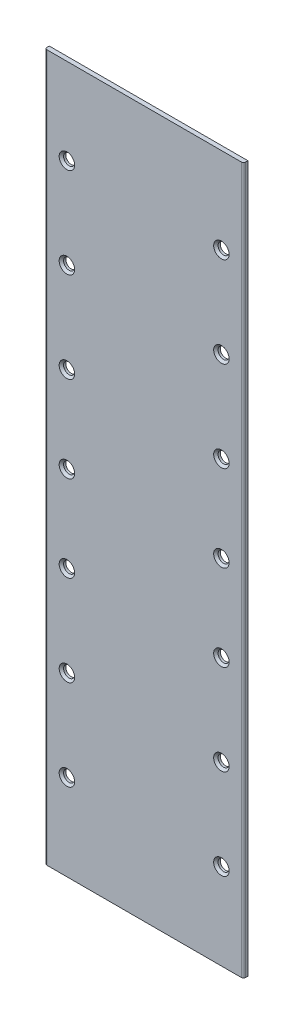
SolidWorks part; units mm, degrees
ref_plane "Plan de face" through (0, 0, 0) normal (0, 0, 1) x (1, 0, 0)
ref_plane "Plan de dessus" through (0, 0, 0) normal (0, 1, 0) x (1, 0, 0)
ref_plane "Plan de droite" through (0, 0, 0) normal (1, 0, 0) x (0, 0, -1)
sketch "Esquisse1" plane through (0, 0, 0) normal (0, 0, 1) x (1, 0, 0)
  line L1 (45, 160) -> (-45, 160)
  line L2 (45, 160) -> (45, -160)
  line L3 (45, -160) -> (-45, -160)
  line L4 (-45, 160) -> (-45, -160)
  line L5 (45, 160) -> (-45, -160) construction
  line L6 (45, -160) -> (-45, 160) construction
  point P0 (0, 0)
  dimension "D1" = 320
  dimension "D2" = 90
extrude "Boss.-Extru.1" add sketch "Esquisse1" along normal blind 2
sketch "Esquisse2" plane through (0, 0, 2) normal (0, 0, 1) x (1, 0, 0)
  line L0 (45, 160) -> (35, 160)
  line L1 (45, 160) -> (-45, 160) construction
  line L2 (-15.0203, 0) -> (15.0203, 0) construction
  line L4 (35, -80) -> (61.6015, -80) construction
  line L5 (0, 0) -> (0, 26.6297) construction
  line L7 (-35, -80) -> (-61.6015, -80) construction
  circle A0 centre (35, 0) radius 2.5
  circle A1 centre (35, 80) radius 2.5
  circle A2 centre (35, -80) radius 2.5
  circle A3 centre (35, -120.982) radius 2.5
  circle A4 centre (35, 120.982) radius 2.5
  circle A5 centre (35, -39.018) radius 2.5
  circle A6 centre (35, 39.018) radius 2.5
  circle A7 centre (35, 80) radius 2.5
  circle A8 centre (-35, -39.018) radius 2.5
  circle A9 centre (-35, -120.982) radius 2.5
  circle A10 centre (-35, -80) radius 2.5
  circle A11 centre (-35, 0) radius 2.5
  circle A12 centre (-35, 80) radius 2.5
  circle A13 centre (-35, 39.018) radius 2.5
  circle A14 centre (-35, 120.982) radius 2.5
  circle A15 centre (-35, 80) radius 2.5
  dimension "D1" = 10
extrude "Enlèv. mat.-Extru.1" cut sketch "Esquisse2" against normal blind 45 contours A14 | A4 | A1 | A12 | A13 | A6 | A0 | A11 | A8 | A5 | A2 | A10 | A3 | A9
fillet "Congé2" radius 1 2 edges at (-45, 0, 2) (45, 0, 2)
chamfer "Chanfrein1" distance 1 angle 45 14 edges at (37.5, 120.982, 2) (37.5, 80, 2) (37.5, 39.018, 2) (37.5, 0, 2) (37.5, -39.018, 2) (37.5, -80, 2) (37.5, -120.982, 2) (-32.5, 120.982, 2) (-32.5, 80, 2) (-32.5, 39.018, 2) (-32.5, 0, 2) (-32.5, -39.018, 2) (-32.5, -80, 2) (-32.5, -120.982, 2)
